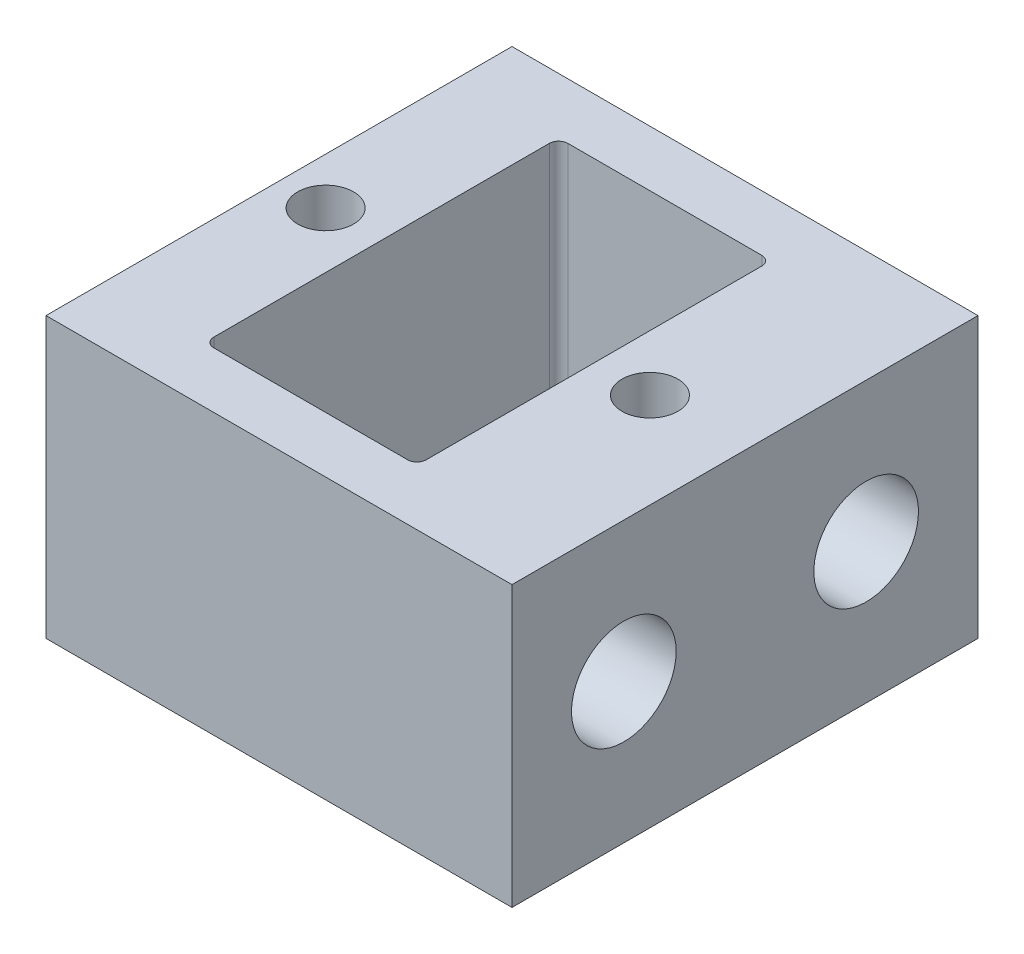
SolidWorks part; units mm, degrees
ref_plane "Front Plane" through (0, 0, 0) normal (0, 0, 1) x (1, 0, 0)
ref_plane "Top Plane" through (0, 0, 0) normal (0, 1, 0) x (1, 0, 0)
ref_plane "Right Plane" through (0, 0, 0) normal (1, 0, 0) x (0, 0, -1)
sketch "Sketch1" plane through (0, 0, 0) normal (0, 1, 0) x (1, 0, 0)
  line L1 (-12.5, 12.5) -> (12.5, 12.5)
  line L2 (-12.5, 12.5) -> (-12.5, -12.5)
  line L3 (-12.5, -12.5) -> (12.5, -12.5)
  line L4 (12.5, 12.5) -> (12.5, -12.5)
  line L5 (-12.5, 12.5) -> (12.5, -12.5) construction
  line L6 (-12.5, -12.5) -> (12.5, 12.5) construction
  point P0 (0, 0)
  dimension "D1" = 25
  dimension "D2" = 25
extrude "Boss-Extrude1" add sketch "Sketch1" along normal blind 15
sketch "Sketch2" plane through (0, 15, 0) normal (0, 1, 0) x (1, 0, 0)
  line L4 (-12.5, 12.5) -> (-12.5, -12.5) construction
  line L5 (-7, 9.5) -> (4.4, -9.5) construction
  line L21 (4.4, -9.5) -> (4.4, 9.5)
  line L22 (-7, 9.5) -> (4.4, 9.5)
  line L24 (-7, -9.5) -> (4.4, -9.5)
  line L27 (-7, 9.5) -> (-7, -9.5)
  point P2 (-7, 0)
  dimension "D3" = 5.5
  dimension "D2" = 19
  dimension "D1" = 11.4
extrude "Cut-Extrude1" cut sketch "Sketch2" against normal through all
hole_wizard "M3 Clearance Hole1" positions "Sketch3" profile "Sketch4" hole size "M3" standard "ANSI Metric" end condition through all
sketch "Sketch3" plane through (0, 15, 0) normal (0, 1, 0) x (1, 0, 0)
  line L0 (-12.5, 12.5) -> (-12.5, -12.5) construction
  point P0 (-10, 0)
  point P3 (7.4, 0)
  dimension "D1" = 17.4
  dimension "D2" = 2.5
sketch "Sketch4" plane through (-10, 15, 0) normal (1, 0, 0) x (0, 0, 1)
  line L0 (0, 0) -> (0, 15)
  line L1 (0, 15) -> (1.5, 15)
  line L2 (1.5, 15) -> (1.5, 0)
  line L5 (1.5, 0) -> (0, 0)
  line L11 (0, -6.35) -> (0, 107.95) construction
  dimension "Thru Hole Dia." = 3
  dimension "Thru Hole Depth" = 15
hole_wizard "for m4 heat set" positions "Sketch6" profile "Sketch7" hole size "#2" standard "ANSI Inch" end condition up to next
sketch "Sketch6" plane through (12.5, 0, 0) normal (1, 0, 0) x (0, 0, -1)
  line L0 (-12.5, 0) -> (12.5, 0) construction
  line L3 (-12.5, 15) -> (12.5, 15) construction
  line L4 (6.5, 7.5) -> (-6.5, 7.5) construction
  point P0 (-6.5, 7.5)
  point P3 (6.5, 7.5)
  point P16 (0, 15)
  point P25 (0, 7.5)
  dimension "D2" = 13
  dimension "D3" = 7.5
sketch "Sketch7" plane through (12.5, 7.5, 6.5) normal (0, 1, 0) x (0, 0, -1)
  line L0 (0, 0) -> (0, 8.1)
  line L1 (0, 8.1) -> (2.8067, 8.1)
  line L2 (2.8067, 8.1) -> (2.8067, 0)
  line L5 (2.8067, 0) -> (0, 0)
  line L11 (0, -6.35) -> (0, 107.95) construction
  dimension "Thru Hole Dia." = 5.6134
  dimension "Thru Hole Depth" = 8.1
sketch "Sketch5" plane through (12.5, 0, 0) normal (1, 0, 0) x (0, 0, -1)
  line L0 (-5, 7.5) -> (5, 7.5) construction
  line L1 (-12.5, 15) -> (12.5, 15) construction
  line L2 (12.5, 15) -> (12.5, 0) construction
  point P0 (-5, 7.5)
  point P1 (5, 7.5)
  point P6 (0, 15)
  point P7 (0, 7.5)
  point P11 (12.5, 7.5)
  dimension "D1" = 10
fillet "Fillet1" radius 0.5 4 edges at (4.4, 7.5, -9.5) (-7, 7.5, 9.5) (-7, 7.5, -9.5) (4.4, 7.5, 9.5)
